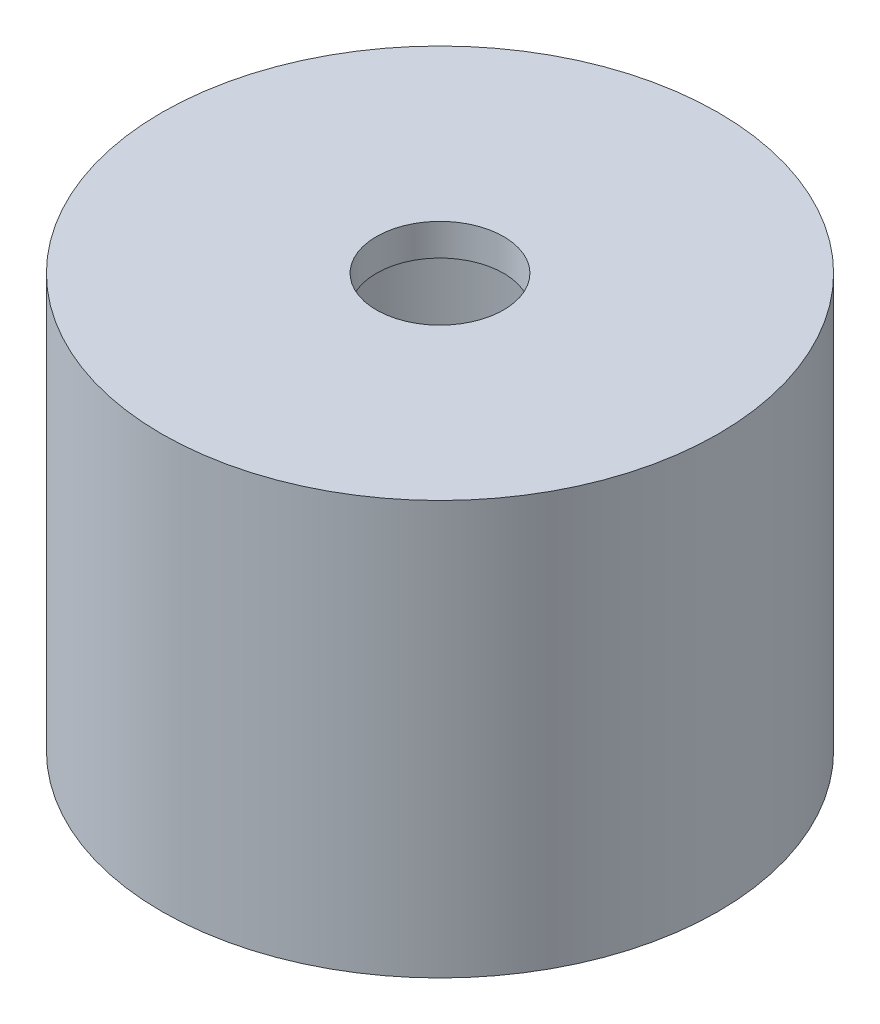
SolidWorks part; units mm, degrees
ref_plane "Plan de face" through (0, 0, 0) normal (0, 0, 1) x (1, 0, 0)
ref_plane "Plan de dessus" through (0, 0, 0) normal (0, 1, 0) x (1, 0, 0)
ref_plane "Plan de droite" through (0, 0, 0) normal (1, 0, 0) x (0, 0, -1)
sketch "Esquisse1" plane through (0, 0, 0) normal (0, 0, 1) x (1, 0, 0)
  line L0 (-8.5, 3) -> (-4, 3) construction
  line L1 (-17.5, 5) -> (-4, 5)
  line L2 (-17.5, -21) -> (-11, -21)
  line L3 (-17.5, 5) -> (-17.5, -21)
  line L4 (-4, 5) -> (-4, 3)
  line L5 (-11, 3) -> (-4, 3)
  line L6 (0, 0) -> (0, -19) construction
  line L7 (-8.5, 5) -> (-4, 5) construction
  line L8 (-11, 3) -> (-11, -21)
revolve "Révolution1" add sketch "Esquisse1" angle 360 about L6
sketch "Esquisse2" plane through (0, 0, 0) normal (1, 0, 0) x (0, 0, -1)
  circle A0 centre (0, -13.5) radius 2
extrude "Extrusion1" cut sketch "Esquisse2" against normal up to next
